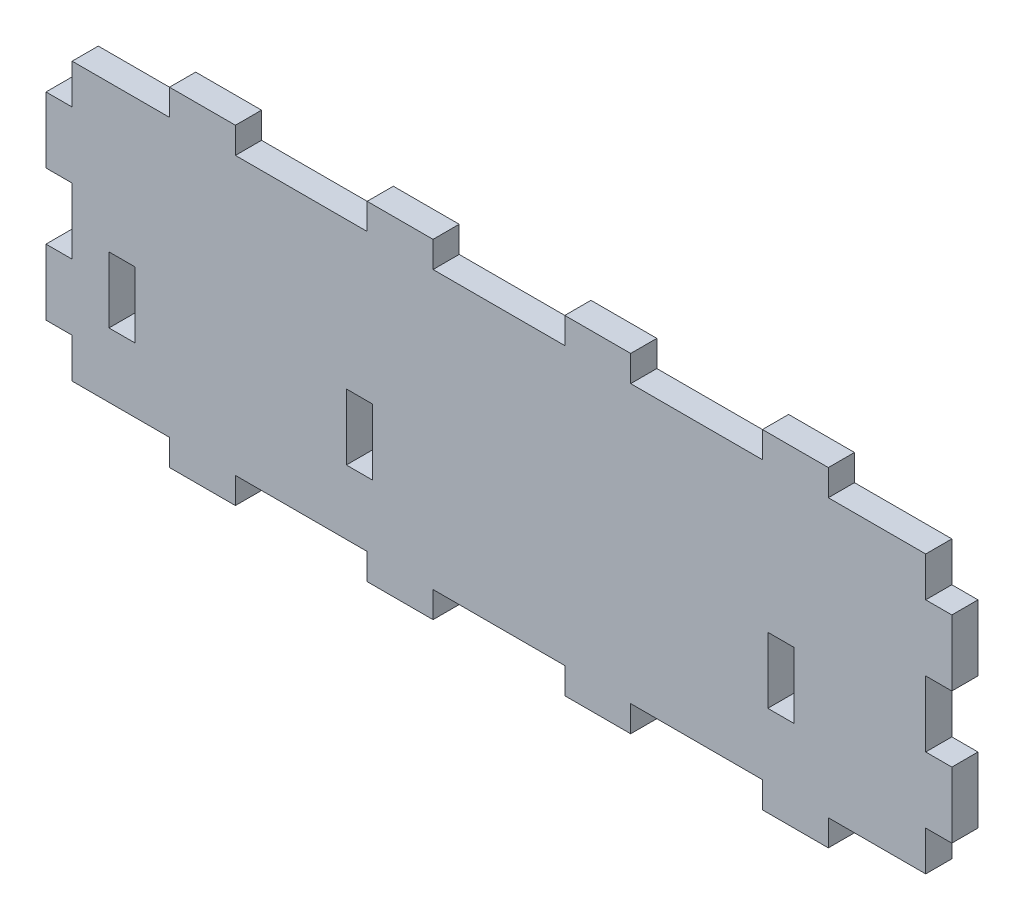
SolidWorks part; units mm, degrees
ref_plane "Front Plane" through (0, 0, 0) normal (0, 0, 1) x (1, 0, 0)
ref_plane "Top Plane" through (0, 0, 0) normal (0, 1, 0) x (1, 0, 0)
ref_plane "Right Plane" through (0, 0, 0) normal (1, 0, 0) x (0, 0, -1)
sketch "Sketch1" plane through (0, 0, 0) normal (0, 0, 1) x (1, 0, 0)
  line L1 (0, 0) -> (110, 0)
  line L2 (0, 0) -> (0, -40)
  line L3 (0, -40) -> (110, -40)
  line L4 (110, 0) -> (110, -40)
  dimension "D1" = 40
  dimension "D2" = 110
extrude "Boss-Extrude1" add sketch "Sketch1" along normal blind 3.175
sketch "Sketch6" plane through (0, 0, 0) normal (0, 0, -1) x (-1, 0, 0)
  line L0 (-55, 0) -> (-55, -40) construction
  line L1 (-110, 0) -> (0, 0) construction
  line L2 (0, -40) -> (-110, -40) construction
  line L3 (-110, -20) -> (0, -20) construction
  line L4 (-110, -40) -> (-110, 0) construction
  line L5 (0, 0) -> (0, -40) construction
  line L6 (-95, -40) -> (-95, -36.825)
  line L7 (-63, -40) -> (-47, -40)
  line L8 (-110, -36.825) -> (-95, -36.825)
  line L9 (-63, -36.825) -> (-47, -36.825)
  line L10 (-47, -40) -> (-47, -36.825)
  line L11 (-39, -40) -> (-23, -40)
  line L12 (-39, -40) -> (-39, -36.825)
  line L13 (-39, -36.825) -> (-23, -36.825)
  line L14 (-23, -40) -> (-23, -36.825)
  line L15 (0, -40) -> (-15, -40)
  line L16 (0, -40) -> (0, -36.825)
  line L17 (0, -36.825) -> (-15, -36.825)
  line L18 (-15, -40) -> (-15, -36.825)
  line L19 (-110, -40) -> (-110, -36.825)
  line L20 (-110, -40) -> (-95, -40)
  line L21 (-87, -40) -> (-87, -36.825)
  line L22 (-71, -36.825) -> (-87, -36.825)
  line L23 (-71, -40) -> (-71, -36.825)
  line L24 (-71, -40) -> (-87, -40)
  line L25 (-63, -40) -> (-63, -36.825)
  line L26 (-63, 0) -> (-63, -3.175)
  line L27 (-71, 0) -> (-87, 0)
  line L28 (-71, 0) -> (-71, -3.175)
  line L29 (-71, -3.175) -> (-87, -3.175)
  line L30 (-87, 0) -> (-87, -3.175)
  line L31 (-110, 0) -> (-95, 0)
  line L32 (-110, 0) -> (-110, -3.175)
  line L33 (-15, 0) -> (-15, -3.175)
  line L34 (0, -3.175) -> (-15, -3.175)
  line L35 (0, 0) -> (0, -3.175)
  line L36 (0, 0) -> (-15, 0)
  line L37 (-23, 0) -> (-23, -3.175)
  line L38 (-39, -3.175) -> (-23, -3.175)
  line L39 (-39, 0) -> (-39, -3.175)
  line L40 (-39, 0) -> (-23, 0)
  line L41 (-47, 0) -> (-47, -3.175)
  line L42 (-63, -3.175) -> (-47, -3.175)
  line L43 (-110, -3.175) -> (-95, -3.175)
  line L44 (-63, 0) -> (-47, 0)
  line L45 (-95, 0) -> (-95, -3.175)
  point P34 (-55, -36.825)
  point P54 (-55, -3.175)
  dimension "D1" = 8
  dimension "D2" = 3.175
  dimension "D3" = 16
  dimension "D4" = 3.175
  dimension "D5" = 8
  dimension "D6" = 3.175
  dimension "D7" = 8
extrude "Cut-Extrude5" cut sketch "Sketch6" against normal up to next
sketch "Sketch7" plane through (0, 0, 0) normal (0, 0, -1) x (-1, 0, 0)
  line L0 (-110, -20) -> (0, -20) construction
  line L1 (-110, -36.825) -> (-110, -3.175) construction
  line L2 (0, -3.175) -> (0, -36.825) construction
  line L3 (-106.825, -36.825) -> (-106.825, -32)
  line L4 (-110, -32) -> (-106.825, -32)
  line L5 (-110, -24) -> (-110, -16)
  line L6 (-110, -16) -> (-106.825, -16)
  line L7 (-106.825, -24) -> (-106.825, -16)
  line L8 (-110, -3.175) -> (-106.825, -3.175)
  line L9 (-110, -3.175) -> (-110, -8)
  line L10 (-110, -8) -> (-106.825, -8)
  line L11 (-106.825, -3.175) -> (-106.825, -8)
  line L12 (-110, -36.825) -> (-110, -32)
  line L13 (-110, -36.825) -> (-106.825, -36.825)
  line L14 (-110, -24) -> (-106.825, -24)
  line L15 (-55, -3.175) -> (-55, -36.825) construction
  line L16 (-63, -3.175) -> (-47, -3.175) construction
  line L17 (-47, -36.825) -> (-63, -36.825) construction
  line L18 (0, -24) -> (-3.175, -24)
  line L19 (0, -36.825) -> (-3.175, -36.825)
  line L20 (0, -36.825) -> (0, -32)
  line L21 (-3.175, -3.175) -> (-3.175, -8)
  line L22 (0, -8) -> (-3.175, -8)
  line L23 (0, -3.175) -> (0, -8)
  line L24 (0, -3.175) -> (-3.175, -3.175)
  line L25 (-3.175, -24) -> (-3.175, -16)
  line L26 (0, -16) -> (-3.175, -16)
  line L27 (0, -24) -> (0, -16)
  line L28 (0, -32) -> (-3.175, -32)
  line L29 (-3.175, -36.825) -> (-3.175, -32)
  point P19 (-106.825, -20)
  point P38 (-3.175, -20)
  dimension "D1" = 4
  dimension "D2" = 3.175
  dimension "D3" = 3.175
  dimension "D4" = 8
extrude "Cut-Extrude6" cut sketch "Sketch7" against normal up to next
sketch "Sketch8" plane through (0, 0, 0) normal (0, 0, -1) x (-1, 0, 0)
  line L0 (-39.65, -28.995) -> (-36.475, -28.995)
  line L1 (-90.825, -28.995) -> (-87.65, -28.995)
  line L2 (-90.825, -28.995) -> (-90.825, -20.995)
  line L3 (-90.825, -20.995) -> (-87.65, -20.995)
  line L4 (-87.65, -28.995) -> (-87.65, -20.995)
  line L5 (-39.65, -28.995) -> (-39.65, -20.995)
  line L6 (-39.65, -20.995) -> (-36.475, -20.995)
  line L7 (-36.475, -28.995) -> (-36.475, -20.995)
  line L8 (-10.825, -28.995) -> (-7.65, -28.995)
  line L9 (-10.825, -28.995) -> (-10.825, -20.995)
  line L10 (-10.825, -20.995) -> (-7.65, -20.995)
  line L11 (-7.65, -28.995) -> (-7.65, -20.995)
  point P0 (-90.825, -28.995)
  point P7 (-39.65, -28.995)
  point P12 (-10.825, -28.995)
  dimension "D1" = 16
  dimension "D2" = 7.83
  dimension "D3" = 8
  dimension "D4" = 3.175
  dimension "D6" = 48
  dimension "D8" = 25.65
  dimension "D5" = 2
  dimension "D7" = 2
extrude "Cut-Extrude7" cut sketch "Sketch8" against normal up to next
